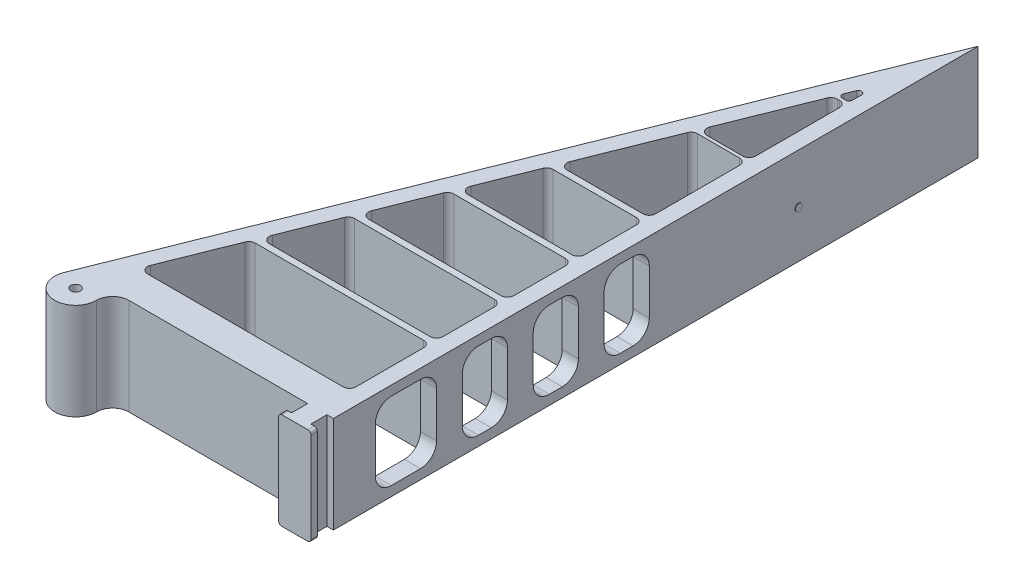
SolidWorks part; units mm, degrees
material "PVC 0.007 Plasticized"
ref_plane "Front Plane" through (0, 0, 0) normal (0, 0, 1) x (1, 0, 0)
ref_plane "Top Plane" through (0, 0, 0) normal (0, 1, 0) x (1, 0, 0)
ref_plane "Right Plane" through (0, 0, 0) normal (1, 0, 0) x (0, 0, -1)
sketch "Sketch1" plane through (0, 0, 0) normal (0, 1, 0) x (1, 0, 0)
  line L0 (0, 0) -> (-80, 0)
  line L1 (-80, 0) -> (0, 200)
  line L2 (0, 200) -> (0, 0)
  line L3 (-5, 10) -> (-70.6148, 10)
  line L4 (-70.6148, 10) -> (-5, 174.0371)
  line L5 (-5, 174.0371) -> (-5, 10)
  dimension "D1" = 80
  dimension "D2" = 200
  dimension "D3" = 5
  dimension "D4" = 10
  dimension "D5" = 5
extrude "Boss-Extrude1" add sketch "Sketch1" along normal blind 30
sketch "Sketch2" plane through (0, 0, 0) normal (0, 1, 0) x (1, 0, 0)
  line L0 (-5, 35) -> (-60.6148, 35)
  line L1 (-5, 10) -> (-5, 174.0371) construction
  line L2 (-5, 174.0371) -> (-70.6148, 10) construction
  line L3 (-60.6148, 35) -> (-59.8148, 37)
  line L4 (-59.8148, 37) -> (-5, 37)
  line L5 (-5, 37) -> (-5, 35)
  line L6 (-70.6148, 10) -> (-5, 10) construction
  line L7 (-51.0148, 59) -> (-51.8148, 57)
  line L8 (-51.8148, 57) -> (-5, 57)
  line L9 (-5, 57) -> (-5, 59)
  line L10 (-5, 59) -> (-51.0148, 59)
  line L11 (-43.0148, 79) -> (-5, 79)
  line L12 (-5, 79) -> (-5, 81)
  line L13 (-5, 81) -> (-42.2148, 81)
  line L14 (-42.2148, 81) -> (-43.0148, 79)
  line L15 (-34.2148, 101) -> (-33.4148, 103)
  line L16 (-33.4148, 103) -> (-5, 103)
  line L17 (-5, 103) -> (-5, 101)
  line L18 (-5, 101) -> (-34.2148, 101)
  line L19 (-21.4148, 133) -> (-21.0148, 134)
  line L20 (-21.0148, 134) -> (-5, 134)
  line L21 (-5, 134) -> (-5, 133)
  line L22 (-5, 133) -> (-21.4148, 133)
  line L23 (-9.0148, 164) -> (-8.6148, 165)
  line L24 (-5, 174.0371) -> (-70.6148, 10) construction
  line L25 (-8.6148, 165) -> (-5, 165)
  line L26 (-5, 165) -> (-5, 164)
  line L27 (-5, 164) -> (-9.0148, 164)
  dimension "D1" = 2
  dimension "D2" = 25
  dimension "D4" = 20
  dimension "D7" = 20
  dimension "D8" = 20
  dimension "D9" = 1
  dimension "D10" = 30
  dimension "D12" = 30
extrude "Boss-Extrude2" add sketch "Sketch2" along normal up to surface (30 mm away) up to face at (-26.6667, 30, -66.6667)
sketch "Sketch3" plane through (0, 0, 0) normal (0, 1, 0) x (1, 0, 0)
  line L0 (-2, 0) -> (-2, -5)
  line L1 (-80, 0) -> (0, 0) construction
  line L2 (-2, -5) -> (0, -5)
  line L3 (0, -5) -> (0, -7)
  line L4 (0, -7) -> (-10, -7)
  line L5 (-10, -7) -> (-10, -5)
  line L6 (-10, -5) -> (-8, -5)
  line L7 (-8, -5) -> (-8, 0)
  line L8 (-8, 0) -> (-2, 0)
  line L9 (-80, 0) -> (-81.0344, -2.586)
  line L10 (0, 200) -> (-80, 0) construction
  line L11 (-68.4993, -5) -> (-68.4993, 0) construction
  line L12 (-80, 0) -> (-63.4993, 0)
  circle A0 centre (-74.9993, -5) radius 1.5
  arc A1 (-81.0344, -2.586) -> (-68.4993, -5) centre (-74.9993, -5) ccw
  arc A2 (-68.4993, -5) -> (-63.4993, 0) centre (-63.4993, -5) cw
  dimension "D4" = 3
  dimension "D5" = 5
  dimension "D1" = 10
  dimension "D2" = 5
  dimension "D3" = 2
  dimension "D6" = 5
  dimension "D7" = 2
extrude "Boss-Extrude3" add sketch "Sketch3" along normal up to surface (30 mm away) up to face at (-6.2049, 30, -168.0124)
sketch "Sketch4" plane through (0, 0, 0) normal (1, 0, 0) x (0, 0, -1)
  circle A0 centre (144.3192, 14.5862) radius 1.1003
extrude "Boss-Extrude4" add sketch "Sketch4" along normal blind 0.1
sketch "Sketch5" plane through (-5, 0, 0) normal (-1, 0, 0) x (0, 0, 1)
  line L24 (-84, 27) -> (-98, 27)
  line L25 (-98, 27) -> (-98, 3)
  line L26 (-98, 3) -> (-84, 3)
  line L27 (-84, 3) -> (-84, 27)
  line L32 (-84, 27) -> (-98, 27)
  line L33 (-98, 27) -> (-98, 3)
  line L34 (-98, 3) -> (-84, 3)
  line L35 (-84, 3) -> (-84, 27)
  line L40 (-62, 27) -> (-76, 27)
  line L41 (-76, 27) -> (-76, 3)
  line L42 (-76, 3) -> (-62, 3)
  line L43 (-62, 3) -> (-62, 27)
  line L44 (-62, 27) -> (-76, 27)
  line L45 (-76, 27) -> (-76, 3)
  line L46 (-76, 3) -> (-62, 3)
  line L47 (-62, 3) -> (-62, 27)
  line L52 (-40, 27) -> (-54, 27)
  line L53 (-54, 27) -> (-54, 3)
  line L54 (-54, 3) -> (-40, 3)
  line L55 (-40, 3) -> (-40, 27)
  line L56 (-40, 27) -> (-54, 27)
  line L57 (-54, 27) -> (-54, 3)
  line L58 (-54, 3) -> (-40, 3)
  line L59 (-40, 3) -> (-40, 27)
  line L64 (-13, 27) -> (-32, 27)
  line L65 (-32, 27) -> (-32, 3)
  line L66 (-32, 3) -> (-13, 3)
  line L67 (-13, 3) -> (-13, 27)
  line L68 (-13, 27) -> (-32, 27)
  line L69 (-32, 27) -> (-32, 3)
  line L70 (-32, 3) -> (-13, 3)
  line L71 (-13, 3) -> (-13, 27)
  dimension "D1" = 3
  dimension "D2" = 3
  dimension "D3" = 3
  dimension "D4" = 3
extrude "Cut-Extrude1" cut sketch "Sketch5" against normal through all
fillet "Fillet1" radius 2 24 edges at (-5, 15, -10) (-70.6148, 15, -10) (-60.6148, 15, -35) (-5, 15, -35) (-5, 15, -37) (-59.8148, 15, -37) (-51.8148, 15, -57) (-5, 15, -57) (-5, 15, -59) (-51.0148, 15, -59) (-43.0148, 15, -79) (-5, 15, -79) (-5, 15, -81) (-42.2148, 15, -81) (-34.2148, 15, -101) (-5, 15, -101) (-33.4148, 15, -103) (-5, 15, -103) (-5, 15, -133) (-21.4148, 15, -133) (-21.0148, 15, -134) (-5, 15, -134) (-5, 15, -164) (-9.0148, 15, -164)
fillet "Fillet2" radius 1 3 edges at (-8.6148, 15, -165) (-5, 15, -165) (-5, 15, -174.0371)
fillet "Fillet3" radius 5 16 edges at (-2.5, 3, -32) (-2.5, 27, -32) (-2.5, 27, -13) (-2.5, 3, -13) (-2.5, 3, -40) (-2.5, 3, -54) (-2.5, 27, -54) (-2.5, 27, -40) (-2.5, 27, -62) (-2.5, 27, -76) (-2.5, 3, -76) (-2.5, 3, -62) (-2.5, 3, -84) (-2.5, 27, -84) (-2.5, 27, -98) (-2.5, 3, -98)
fillet "Fillet4" radius 1 4 edges at (0, 0, 6) (-10, 0, 6) (-10, 30, 6) (0, 30, 6)
